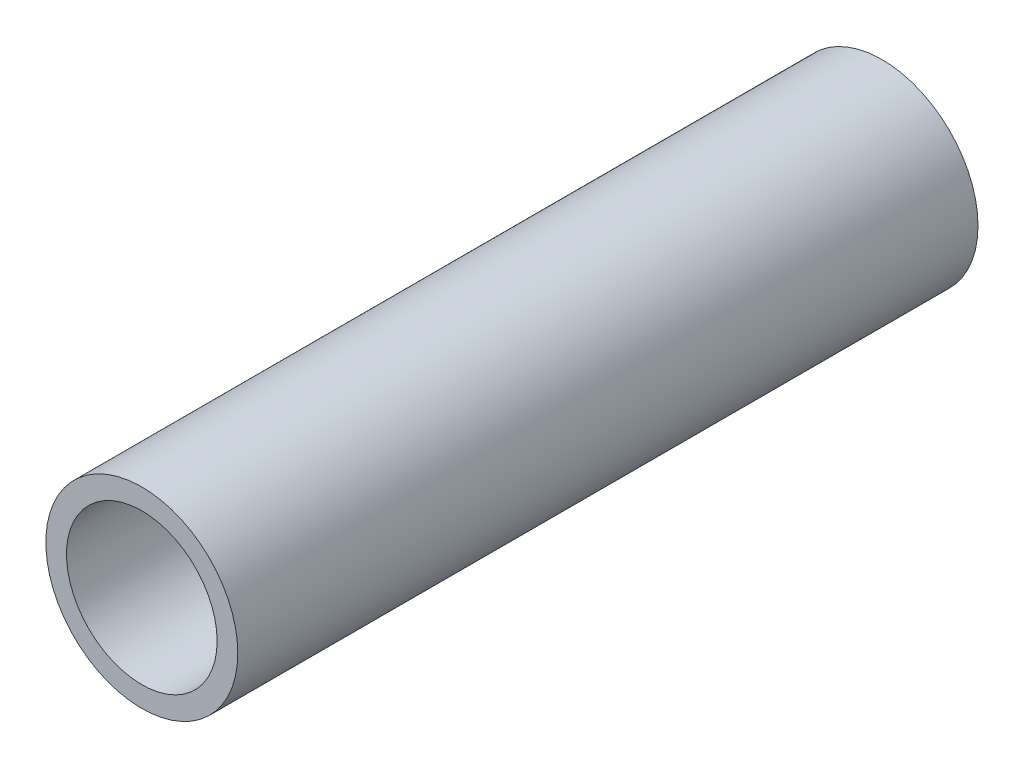
SolidWorks part; units mm, degrees
material "PVC 0.007 Plasticized"
ref_plane "Front Plane" through (0, 0, 0) normal (0, 0, 1) x (1, 0, 0)
ref_plane "Top Plane" through (0, 0, 0) normal (0, 1, 0) x (1, 0, 0)
ref_plane "Right Plane" through (0, 0, 0) normal (1, 0, 0) x (0, 0, -1)
sketch "Sketch1" plane through (0, 0, 0) normal (0, 0, 1) x (1, 0, 0)
  line L0 (10.4648, 0) -> (13.335, 0) construction
  circle A0 centre (0, 0) radius 13.335 construction
  circle A1 centre (0, 0) radius 10.4648 construction
  dimension "ID" = 20.9296
  dimension "OD" = 26.67
  dimension "Wall Thickness" = 2.8702
sketch "Sketch2" plane through (0, 0, 0) normal (1, 0, 0) x (0, 0, -1)
  line L0 (-762, 0) -> (762, 0) construction
  line L1 (-728.6625, 13.335) -> (-728.6625, -13.335) construction
  line L2 (728.6625, 13.335) -> (728.6625, -13.335) construction
  point P4 (0, 0)
  point P8 (-728.6625, 0)
  point P11 (728.6625, 0)
  dimension "Length" = 1524
  dimension "D1" = 33.3375
  dimension "D2" = 33.3375
  dimension "D3" = 26.67
sketch "Sketch3" plane through (0, 0, 0) normal (0, 0, 1) x (1, 0, 0)
  circle A0 centre (0, 0) radius 13.335
  circle A1 centre (0, 0) radius 13.335 construction
  circle A2 centre (0, 0) radius 10.4648 construction
  circle A3 centre (0, 0) radius 10.4648
extrude "Boss-Extrude1" add sketch "Sketch3" along normal up to vertex (762 mm away) and the other way up to vertex (762 mm away) up to point (0, 0, 762) other way up to point (0, 0, -762)
sketch "Sketch4" plane through (0, 0, 762) normal (0, 0, 1) x (1, 0, 0)
  circle A0 centre (0, 0) radius 10.4648 construction
  circle A1 centre (0, 0) radius 13.335 construction
  circle A2 centre (0, 0) radius 10.4648
  circle A3 centre (0, 0) radius 13.335
extrude "Cut-Extrude2" cut sketch "Sketch4" against normal offset from surface (1421.1455 mm away) 102.8545 contours A3 up to face at (10.4648, 0, -762)
equation "\"D1@Sketch2\"=\"OD@Sketch1\" * 1.25"
equation "\"D2@Sketch2\"=\"D1@Sketch2\""
equation "\"D3@Sketch2\"= \"OD@Sketch1\""
